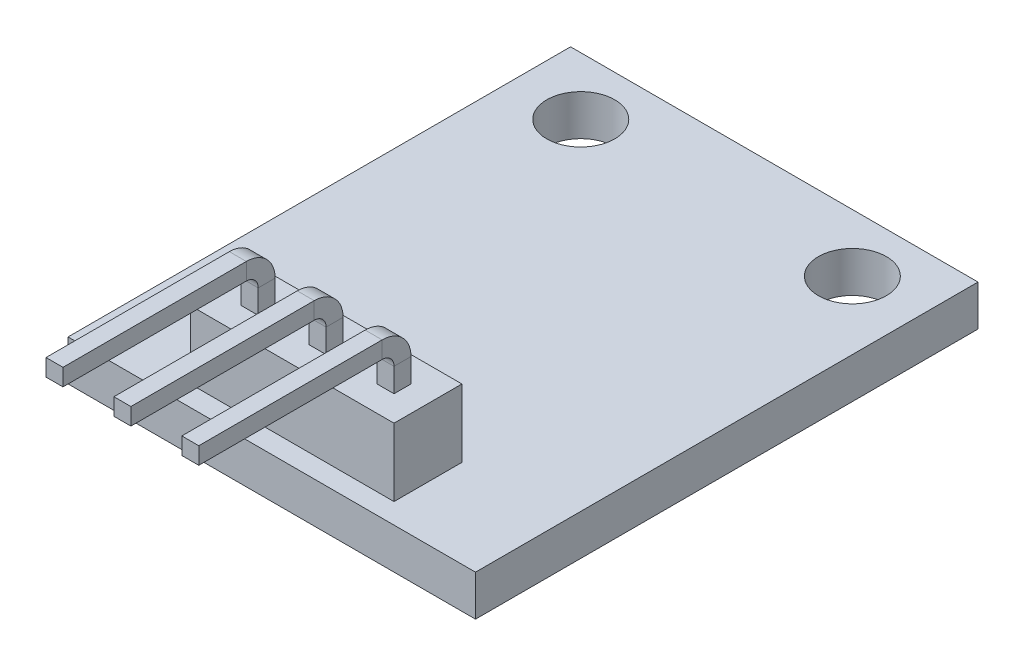
SolidWorks part; units mm, degrees
ref_plane "Front Plane" through (0, 0, 0) normal (0, 0, 1) x (1, 0, 0)
ref_plane "Top Plane" through (0, 0, 0) normal (0, 1, 0) x (1, 0, 0)
ref_plane "Right Plane" through (0, 0, 0) normal (1, 0, 0) x (0, 0, -1)
sketch "Sketch1" plane through (0, 0, 0) normal (0, 1, 0) x (1, 0, 0)
  line L0 (7.62, 9.398) -> (-7.62, -9.398) construction
  line L1 (-7.62, 9.398) -> (7.62, 9.398)
  line L2 (-7.62, 9.398) -> (-7.62, -9.398)
  line L3 (-7.62, -9.398) -> (7.62, -9.398)
  line L4 (7.62, 9.398) -> (7.62, -9.398)
  line L5 (-5.08, 7.239) -> (5.08, 7.239) construction
  line L6 (0, 7.239) -> (0, 0) construction
  circle A0 centre (-5.08, 7.239) radius 1.27
  circle A1 centre (5.08, 7.239) radius 1.27
  dimension "D3" = 2.54
  dimension "D1" = 15.24
  dimension "D2" = 18.796
  dimension "D4" = 10.16
  dimension "D5" = 2.159
extrude "Boss-Extrude1" add sketch "Sketch1" along normal blind 1.524
sketch "Sketch2" plane through (0, 1.524, 0) normal (0, 1, 0) x (1, 0, 0)
  line L0 (3.81, -6.096) -> (-3.81, -8.636) construction
  line L1 (-3.81, -6.096) -> (3.81, -6.096)
  line L2 (-3.81, -6.096) -> (-3.81, -8.636)
  line L3 (-3.81, -8.636) -> (3.81, -8.636)
  line L4 (3.81, -6.096) -> (3.81, -8.636)
  line L5 (0, -7.366) -> (0, 0) construction
  line L6 (-7.62, -9.398) -> (7.62, -9.398) construction
  dimension "D1" = 7.62
  dimension "D2" = 3.302
  dimension "D3" = 2.54
extrude "Boss-Extrude2" add sketch "Sketch2" along normal blind 2.54
sketch "Sketch3" plane through (0, 0, 0) normal (1, 0, 0) x (0, 0, -1)
  line L0 (-7.366, 4.064) -> (-7.366, 4.953)
  line L1 (-6.096, 4.064) -> (-8.636, 4.064) construction
  line L2 (-8.128, 5.715) -> (-14.986, 5.715)
  arc A0 (-7.366, 4.953) -> (-8.128, 5.715) centre (-8.128, 4.953) ccw
  point P5 (-7.366, 4.978)
  point P8 (-8.6717, 4.4093)
  dimension "D3" = 0.762
  dimension "D1" = 1.651
  dimension "D2" = 7.62
ref_plane "Plane1" through (0, 0, 14.986) normal (0, 0, 1) x (1, 0, 0)
sketch "Sketch4" plane through (0, 0, 14.986) normal (0, 0, 1) x (1, 0, 0)
  line L0 (0.3175, 6.0325) -> (-0.3175, 5.3975) construction
  line L1 (-0.3175, 6.0325) -> (0.3175, 6.0325)
  line L2 (-0.3175, 6.0325) -> (-0.3175, 5.3975)
  line L3 (-0.3175, 5.3975) -> (0.3175, 5.3975)
  line L4 (0.3175, 6.0325) -> (0.3175, 5.3975)
  point P6 (0, 5.715)
  dimension "D1" = 0.635
sweep "Sweep1" add profiles "Sketch4" path "Sketch3"
pattern_linear "LPattern1" count 2 spacing 2.54 along (1, 0, 0) count 2 spacing 2.54 along (-1, 0, 0) of "Sweep1"
equation "\"D5@Sketch1\"=0.035 + \"D3@Sketch1\"/2"
